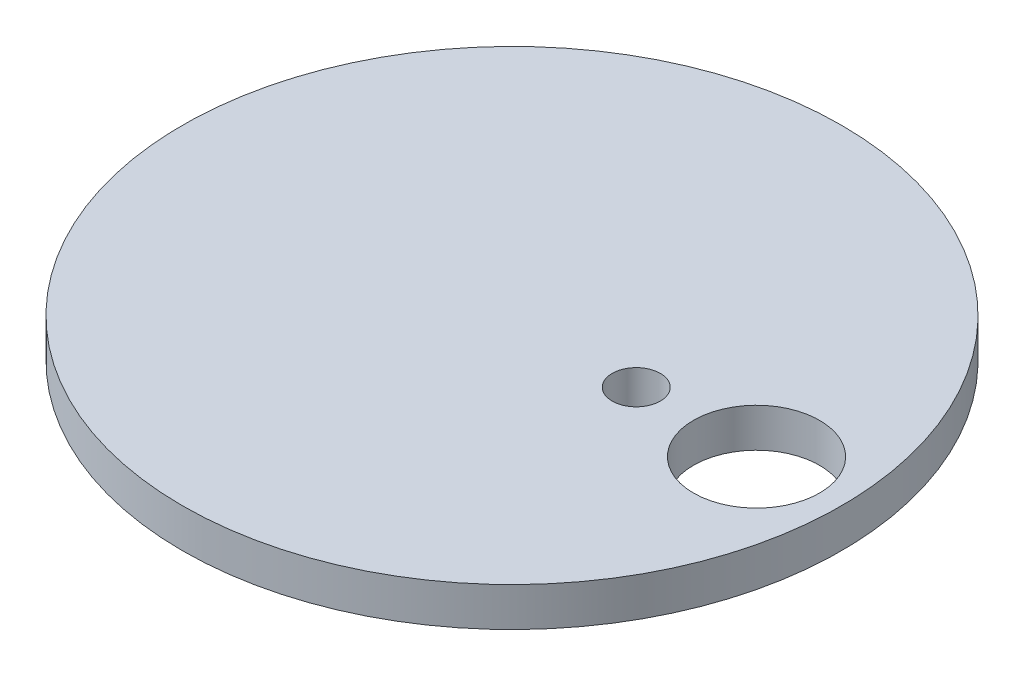
SolidWorks part; units mm, degrees
ref_plane "Front Plane" through (0, 0, 0) normal (0, 0, 1) x (1, 0, 0)
ref_plane "Top Plane" through (0, 0, 0) normal (0, 1, 0) x (1, 0, 0)
ref_plane "Right Plane" through (0, 0, 0) normal (1, 0, 0) x (0, 0, -1)
sketch "Sketch1" plane through (0, 0, 0) normal (0, 1, 0) x (1, 0, 0)
  circle A0 centre (0, 0) radius 4.1275
  circle A1 centre (0, 0) radius 2.8575
  dimension "D1" = 8.255
  dimension "D2" = 5.715
extrude "Boss-Extrude1" add sketch "Sketch1" along normal blind 3.6068
sketch "Sketch3" plane through (0, 3.6068, 0) normal (0, 1, 0) x (1, 0, 0)
  line L0 (0, 0) -> (4.1275, 0) construction
  line L1 (4.1275, 0) -> (5.2896, 0) construction
  line L2 (5.2896, 0) -> (6.5596, 0) construction
  line L3 (6.5596, 0) -> (16.237, 0) construction
  line L4 (16.237, 0) -> (17.399, 0) construction
  circle A0 centre (0, 0) radius 17.399
  circle A1 centre (12.9096, 0) radius 3.3274
  circle A2 centre (6.5596, 0) radius 1.27
  circle A3 centre (0, 0) radius 4.1275 construction
  dimension "D2" = 2.54
  dimension "D4" = 6.35
  dimension "D1" = 34.798
  dimension "D3" = 6.6548
extrude "Boss-Extrude2" add sketch "Sketch3" along normal blind 2.0574
equation "\"plywood thickness\"= 0.19"
equation "\"servo width\"= 0.82"
equation "\"servo length\"= 1.59"
equation "\"servo hole spacing\"= 0.628"
equation "\"servo hole diameter\"= 0.0905"
equation "\"servo mount diameter\"= 0.1565"
equation "\"servo mount side offset\"= 0.1915"
equation "\"servo mount top offset\"= 0.1915"
equation "\"servo planar offset\"= 0.74"
equation "\"leg diameter\"= 0.45"
equation "\"leg length\"= 1.5"
equation "\"arm width\"= 1.5"
equation "\"pan bottom length\"= 4"
equation "\"pan arm length\"= 5"
equation "\"tilt bottom length\"= \"border\" + \"servo hole spacing\" + \"camera height\" + \"plywood thickness\" + \"servo planar offset\""
equation "\"tilt arm length\"= \"pan bottom length\" - \"border\" + \"servo hole spacing\" - \"servo planar offset\" -  \"plywood thickness\" + \"servo hole diameter\"/2"
equation "\"border\"= 0.5"
equation "\"camera height\"= 0.89"
equation "\"crossbrace small length\"= 1"
equation "\"crossbrace small width\"= 1"
equation "\"crossbrace large length\"= 1"
equation "\"crossbrace large width\"= 1"
